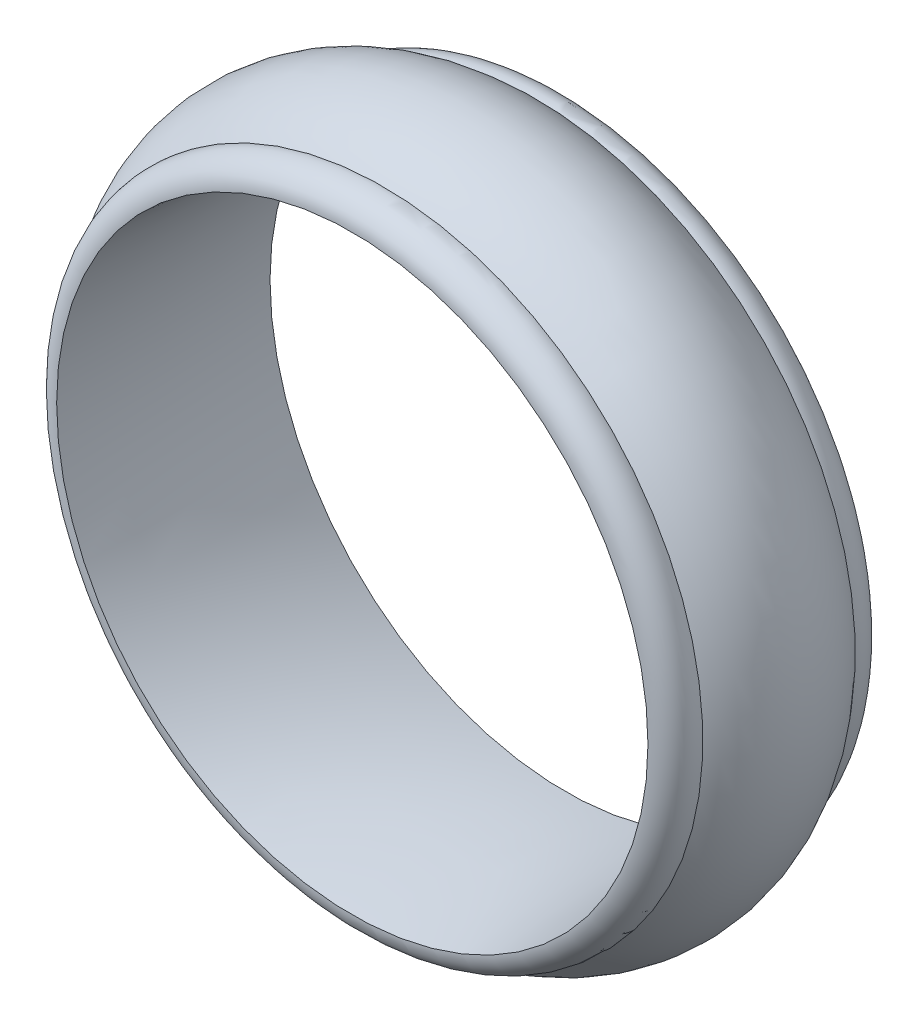
SolidWorks part; units mm, degrees
ref_plane "Спереди" through (0, 0, 0) normal (0, 0, 1) x (1, 0, 0)
ref_plane "Сверху" through (0, 0, 0) normal (0, 1, 0) x (1, 0, 0)
ref_plane "Справа" through (0, 0, 0) normal (1, 0, 0) x (0, 0, -1)
sketch "Эскиз1" plane through (0, 0, 0) normal (1, 0, 0) x (0, 0, -1)
  line L0 (0, 0) -> (-5.5105, 0) construction
  line L1 (0, 0) -> (0, 11.5) construction
  line L2 (3.5, 9.7) -> (-3.5, 9.7) construction
  line L3 (0, 11.5) -> (-3.5, 11.5) construction
  line L4 (-3.5, 11.5) -> (-3.5, 9.7) construction
  arc A0 (-3.5, 9.7) -> (-2.5, 10.5) centre (-2.68, 9.7) cw
  arc A1 (-2.5, 10.5) -> (2.5, 10.5) centre (0, 7.875) cw
  arc A2 (3.5, 9.7) -> (2.5, 10.5) centre (2.68, 9.7) ccw
  arc A3 (-3.5, 9.7) -> (3.5, 9.7) centre (0, 40.225) ccw
  point P7 (0, 9.5)
  point P17 (0, 9.7)
  dimension "D6" = 1.8
  dimension "D1" = 7
  dimension "D2" = 9.5
  dimension "D3" = 5
  dimension "D4" = 2
  dimension "D5" = 0.8
revolve "Повернуть1" add sketch "Эскиз1" angle 360 about L0
